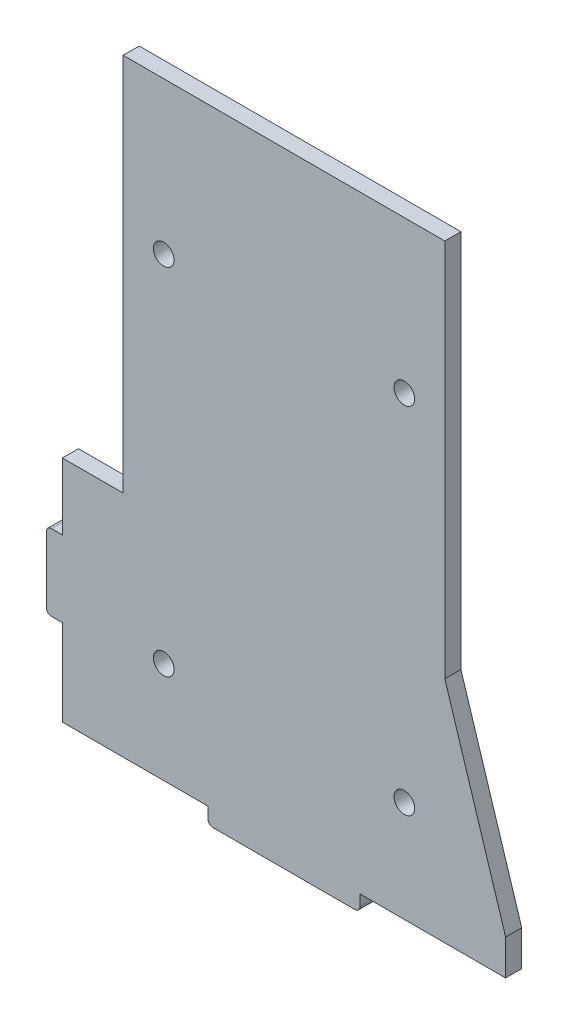
SolidWorks part; units mm, degrees
ref_plane "Front Plane" through (0, 0, 0) normal (0, 0, 1) x (1, 0, 0)
ref_plane "Top Plane" through (0, 0, 0) normal (0, 1, 0) x (1, 0, 0)
ref_plane "Right Plane" through (0, 0, 0) normal (1, 0, 0) x (0, 0, -1)
sketch "Sketch1" plane through (0, 0, 0) normal (0, 0, 1) x (1, 0, 0)
  line L0 (0, -60) -> (0, -55.0578) construction
  line L1 (-31.75, -60) -> (-15, -60)
  line L2 (-31.75, -60) -> (-31.75, -53) construction
  line L3 (-31.75, 60) -> (31.75, 60)
  line L4 (31.75, -14.8424) -> (31.75, 60)
  line L5 (-31.75, -60) -> (31.75, 60) construction
  line L6 (-31.75, 60) -> (31.75, -60) construction
  line L7 (15, -60) -> (15, -63.175)
  line L10 (15, -63.175) -> (-15, -63.175)
  line L11 (-15, -60) -> (-15, -63.175)
  line L12 (15, -60) -> (31.75, -60)
  line L13 (31.75, -60) -> (31.75, -14.8424) construction
  line L15 (31.75, -60) -> (31.75, -14.8424) construction
  line L18 (-31.75, -53) -> (-43.75, -53) construction
  line L20 (-43.75, -53) -> (-43.75, -60)
  line L21 (-43.75, -60) -> (-31.75, -60)
  line L22 (-31.75, -53) -> (-31.75, -14.8424) construction
  line L23 (-31.75, -14.8424) -> (-31.75, 60)
  line L24 (43.75, -60) -> (31.75, -60)
  line L25 (43.75, -53) -> (43.75, -60)
  line L26 (43.75, -53) -> (31.75, -14.8424)
  line L27 (-31.75, -14.8424) -> (-43.75, -14.8424)
  line L28 (-43.75, -14.8424) -> (-43.75, -53)
  point P0 (0, 0)
  dimension "D1" = 63.5
  dimension "D2" = 120
  dimension "D3" = 30
  dimension "D4" = 3.175
  dimension "D7" = 40
  dimension "D8" = 12
  dimension "D9" = 7
extrude "Boss-Extrude1" add sketch "Sketch1" along normal blind 3.175
sketch "Sketch2" plane through (0, 0, 3.175) normal (0, 0, 1) x (1, 0, 0)
  line L0 (-31.75, -40) -> (43.75, -40) construction
  line L3 (-31.75, 30) -> (31.75, 30) construction
  line L4 (31.75, -14.8424) -> (31.75, 60) construction
  line L5 (-43.75, -60) -> (-15, -60) construction
  line L6 (15, -60) -> (43.75, -60) construction
  line L7 (0, 30) -> (0, 25.4672) construction
  line L8 (31.75, -14.8424) -> (31.75, 60) construction
  circle A0 centre (23.75, 30) radius 2.05
  circle A1 centre (23.75, -40) radius 2.05
  circle A2 centre (-23.75, -40) radius 2.05
  circle A3 centre (-23.75, 30) radius 2.05
  dimension "D3" = 4.1
  dimension "D4" = 4.1
  dimension "D1" = 90
  dimension "D2" = 20
  dimension "D5" = 8
  dimension "D6" = 8
extrude "Cut-Extrude1" cut sketch "Sketch2" against normal through all
sketch "Sketch3" plane through (-43.75, 0, 0) normal (-1, 0, 0) x (0, 0, 1)
  line L0 (0, -14.8424) -> (0, -60) construction
  line L1 (0, -43) -> (3.175, -43)
  line L2 (0, -43) -> (0, -28)
  line L3 (0, -28) -> (3.175, -28)
  line L4 (3.175, -43) -> (3.175, -28)
  line L5 (3.175, -14.8424) -> (3.175, -60) construction
  line L6 (3.175, -60) -> (0, -60) construction
  point P10 (1.5875, -43)
  dimension "D1" = 17
  dimension "D2" = 15
extrude "Boss-Extrude2" add sketch "Sketch3" along normal blind 3.175
fillet "Fillet1" radius 1 4 edges at (15, -63.175, 1.5875) (-15, -63.175, 1.5875) (-46.925, -43, 1.5875) (-46.925, -28, 1.5875)
